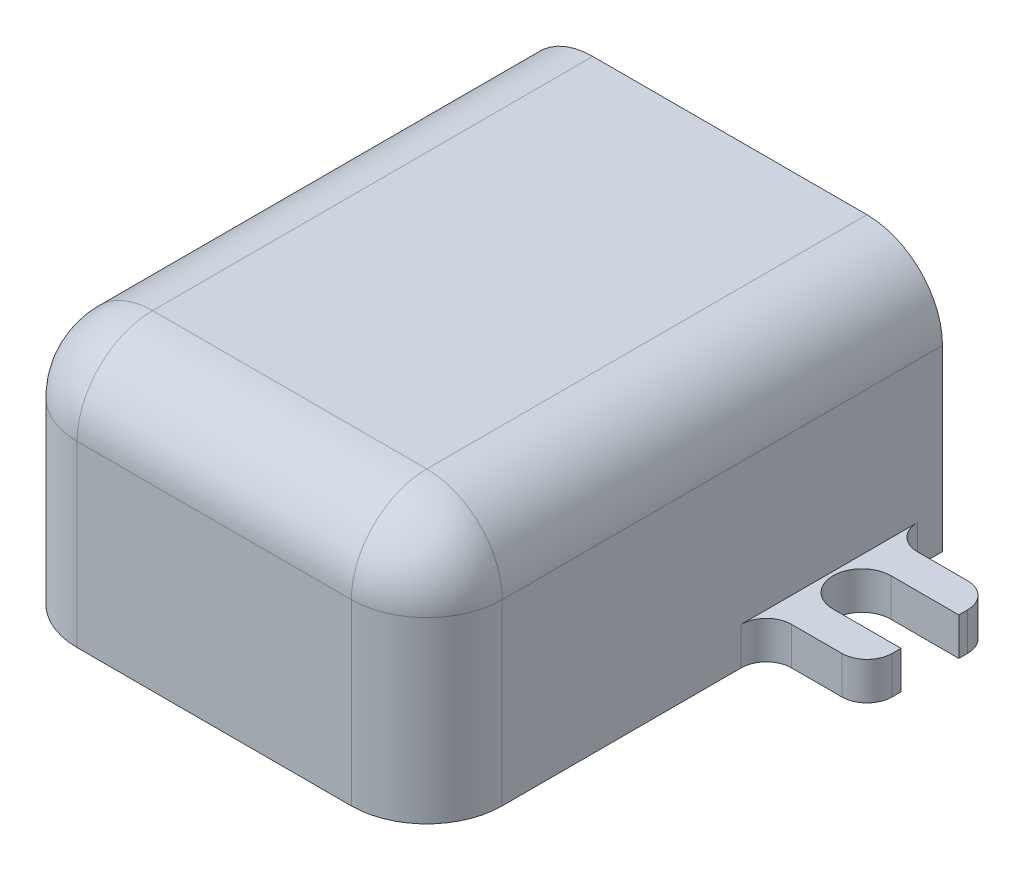
SolidWorks part; units mm, degrees
ref_plane "Front Plane" through (0, 0, 0) normal (0, 0, 1) x (1, 0, 0)
ref_plane "Top Plane" through (0, 0, 0) normal (0, 1, 0) x (1, 0, 0)
ref_plane "Right Plane" through (0, 0, 0) normal (1, 0, 0) x (0, 0, -1)
sketch "Sketch1" plane through (0, 0, 0) normal (0, 1, 0) x (1, 0, 0)
  line L0 (0, 10.25) -> (0, -10.25) construction
  line L1 (-8.45, 10.25) -> (8.45, 10.25)
  line L2 (-8.45, 10.25) -> (-8.45, -10.25)
  line L3 (-8.45, -10.25) -> (8.45, -10.25)
  line L4 (8.45, 10.25) -> (8.45, -10.25)
  line L5 (-8.45, 10.25) -> (8.45, -10.25) construction
  line L6 (-8.45, -10.25) -> (8.45, 10.25) construction
  line L7 (-8.45, 5.75) -> (8.45, 5.75) construction
  line L8 (-9.75, 6.9) -> (-12.45, 6.9)
  line L9 (-8.45, 8.25) -> (-12.45, 8.25)
  line L10 (-8.45, 8.25) -> (-8.45, 3.25)
  line L11 (-8.45, 3.25) -> (-12.45, 3.25)
  line L12 (-12.45, 8.25) -> (-12.45, 3.25)
  line L13 (-8.45, 8.25) -> (-12.45, 3.25) construction
  line L14 (-8.45, 3.25) -> (-12.45, 8.25) construction
  line L15 (-9.75, 4.6) -> (-12.45, 4.6)
  line L16 (9.75, 6.9) -> (12.45, 6.9)
  line L17 (12.45, 8.25) -> (12.45, 3.25)
  line L18 (8.45, 8.25) -> (12.45, 8.25)
  line L19 (9.75, 4.6) -> (12.45, 4.6)
  line L20 (8.45, 3.25) -> (12.45, 3.25)
  circle A0 centre (-9.75, 5.75) radius 1.15
  circle A1 centre (9.75, 5.75) radius 1.15
  point P0 (0, 0)
  point P10 (-12.45, 5.75)
  dimension "D6" = 19.5
  dimension "D7" = 2.3
  dimension "D1" = 20.5
  dimension "D2" = 16.9
  dimension "D3" = 5
  dimension "D4" = 2
  dimension "D5" = 4
extrude "Boss-Extrude1" add sketch "Sketch1" along normal blind 1.5 contours A0 L15 L12 L11 L2 L9 L8 | L4 L1 L2 L3 | L19 A1 L16 L17 L18 L4 L20
sketch "Sketch2" plane through (0, 1.5, 0) normal (0, 1, 0) x (1, 0, 0)
  line L1 (-8.45, 10.25) -> (8.45, 10.25)
  line L2 (-8.45, 10.25) -> (-8.45, -10.25)
  line L3 (-8.45, -10.25) -> (8.45, -10.25)
  line L4 (8.45, 10.25) -> (8.45, -10.25)
extrude "Boss-Extrude2" add sketch "Sketch2" along normal offset from surface (8.6 mm away) 10.1 up to face at (0, 0, -4.6)
fillet "Fillet1" radius 3 5 edges at (-8.45, 10.1, 0) (8.45, 10.1, 0) (-8.45, 5.05, 10.25) (8.45, 5.05, 10.25) (0, 10.1, 10.25)
fillet "Fillet2" radius 1 8 edges at (-8.45, 0.75, -8.25) (-12.45, 0.75, -8.25) (-12.45, 0.75, -3.25) (-8.45, 0.75, -3.25) (8.45, 0.75, -8.25) (12.45, 0.75, -8.25) (12.45, 0.75, -3.25) (8.45, 0.75, -3.25)
sketch "Sketch3" plane through (0, 0, -10.25) normal (0, 0, -1) x (-1, 0, 0)
  line L0 (0, 10.1) -> (0, 0) construction
  line L1 (-5.45, 10.1) -> (5.45, 10.1) construction
  line L2 (0, 5.05) -> (8.45, 5.05) construction
  line L3 (8.45, 7.1) -> (8.45, 0) construction
  line L4 (0, 5.05) -> (-8.45, 5.05) construction
  line L5 (-8.45, 7.1) -> (-8.45, 0) construction
  line L6 (7.5, 6.05) -> (6, 7.55)
  line L7 (-7.5, 7.55) -> (7.5, 7.55)
  line L8 (-7.5, 7.55) -> (-7.5, 2.55)
  line L9 (-7.5, 2.55) -> (7.5, 2.55)
  line L10 (7.5, 7.55) -> (7.5, 2.55)
  line L11 (-7.5, 7.55) -> (7.5, 2.55) construction
  line L12 (-7.5, 2.55) -> (7.5, 7.55) construction
  line L13 (7.5, 4.05) -> (6, 2.55)
  circle A0 centre (-3.6, 5.05) radius 1.5
  circle A1 centre (3.6, 5.05) radius 1.5
  dimension "D6" = 3
  dimension "D1" = 15
  dimension "D2" = 5
  dimension "D3" = 2
  dimension "D4" = 45
  dimension "D5" = 7.2
extrude "Cut-Extrude1" cut sketch "Sketch3" against normal blind 10 contours L13 L10 L6 L7 L8 L9 A1 A0
